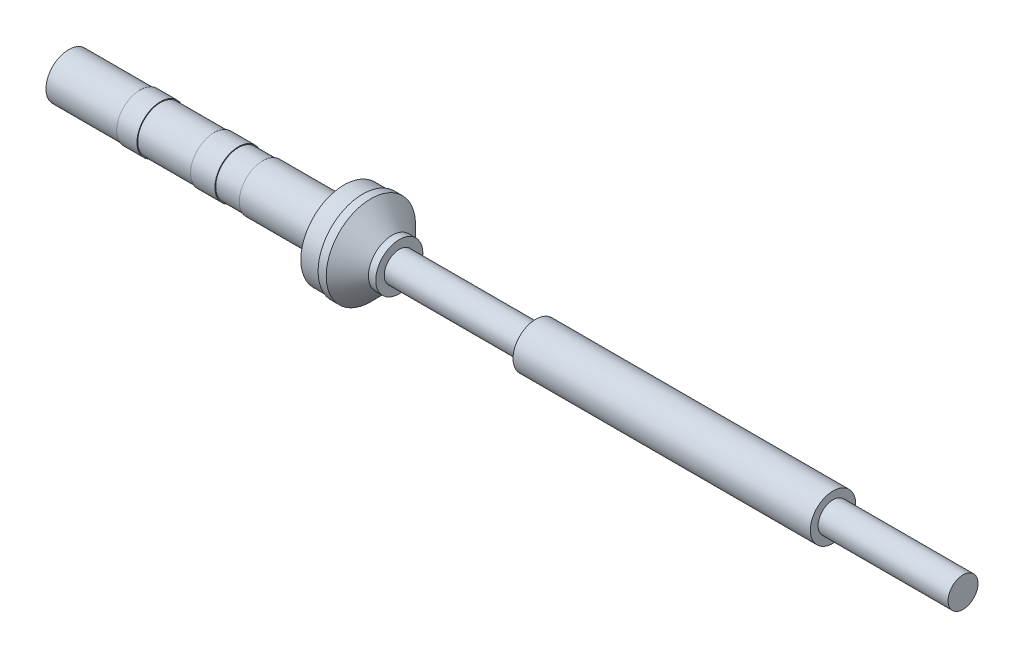
SolidWorks part; units mm, degrees
material "ABS"
ref_plane "Front Plane" through (0, 0, 0) normal (0, 0, 1) x (1, 0, 0)
ref_plane "Top Plane" through (0, 0, 0) normal (0, 1, 0) x (1, 0, 0)
ref_plane "Right Plane" through (0, 0, 0) normal (1, 0, 0) x (0, 0, -1)
sketch "Sketch1" plane through (0, 0, 0) normal (0, 1, 0) x (1, 0, 0)
  line L2 (23.9, -2.8959) -> (33.9, -2.8959)
  line L3 (33.9, -2.8959) -> (33.9, -5.3209)
  line L4 (33.9, -5.3209) -> (36.2, -5.3209)
  line L5 (36.2, -5.3209) -> (36.2, -5.4945)
  line L6 (36.2, -5.4945) -> (37.2, -5.4945)
  line L7 (37.2, -5.4945) -> (39.8, -2.8959)
  line L8 (39.8, -2.8959) -> (40.7, -2.8959)
  line L9 (40.7, -2.8959) -> (40.7, -1.8459)
  line L10 (0, 0) -> (110.1, 0)
  line L11 (40.7, -1.8459) -> (57.5, -1.8459)
  line L12 (57.5, -1.8459) -> (57.5, -2.7945)
  line L13 (57.5, -2.7945) -> (94.1, -2.7945)
  line L14 (94.1, -2.7945) -> (94.1, -1.8459)
  line L15 (94.1, -1.8459) -> (110.1, -1.8459)
  line L16 (110.1, -1.8459) -> (110.1, 0)
  line L17 (0, -2.7945) -> (8.8, -2.7945)
  line L18 (8.8, -2.8959) -> (11.3, -2.8959)
  line L19 (11.3, -2.7945) -> (17.9, -2.7945)
  line L20 (20.9, -2.7945) -> (23.9, -2.7945)
  line L21 (17.9, -2.8959) -> (20.9, -2.8959)
  line L22 (0, -2.7945) -> (0, 0)
  line L23 (8.8, -2.8959) -> (8.8, -2.7945)
  line L24 (11.3, -2.8959) -> (11.3, -2.7945)
  line L25 (17.9, -2.8959) -> (17.9, -2.7945)
  line L26 (20.9, -2.8959) -> (20.9, -2.7945)
  line L27 (23.9, -2.8959) -> (23.9, -2.7945)
revolve "Revolve1" add sketch "Sketch1" angle 360 about L10
sketch "Sketch2" plane through (0, 0, 0) normal (-1, 0, 0) x (0, 0, 1)
  circle A1 centre (0, 0) radius 2.7945
  circle A2 centre (0, 0) radius 2.7945
  dimension "D1" = 0
extrude "Cut-Extrude1" cut sketch "Sketch2" against normal blind 28
sketch "Sketch3" plane through (0, 0, 0) normal (1, 0, 0) x (0, 0, -1)
  circle A0 centre (0, 0) radius 2.7945 construction
  circle A1 centre (0, 0) radius 2.7945
extrude "Boss-Extrude1" add sketch "Sketch3" along normal blind 28 separate body
